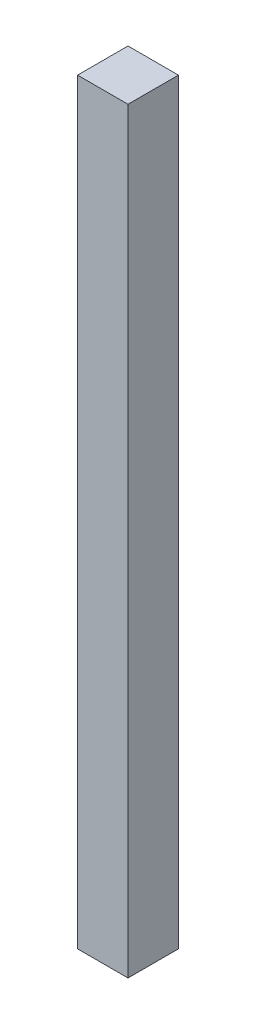
SolidWorks part; units mm, degrees
ref_plane "Front Plane" through (0, 0, 0) normal (0, 0, 1) x (1, 0, 0)
ref_plane "Top Plane" through (0, 0, 0) normal (0, 1, 0) x (1, 0, 0)
ref_plane "Right Plane" through (0, 0, 0) normal (1, 0, 0) x (0, 0, -1)
sketch "Sketch1" plane through (0, 0, 0) normal (0, 1, 0) x (1, 0, 0)
  line L1 (0, 0) -> (25.4, 0)
  line L2 (0, 0) -> (0, 25.4)
  line L3 (0, 25.4) -> (25.4, 25.4)
  line L4 (25.4, 0) -> (25.4, 25.4)
  dimension "D1" = 25.4
  dimension "D2" = 25.4
extrude "Boss-Extrude1" add sketch "Sketch1" along normal blind 381
